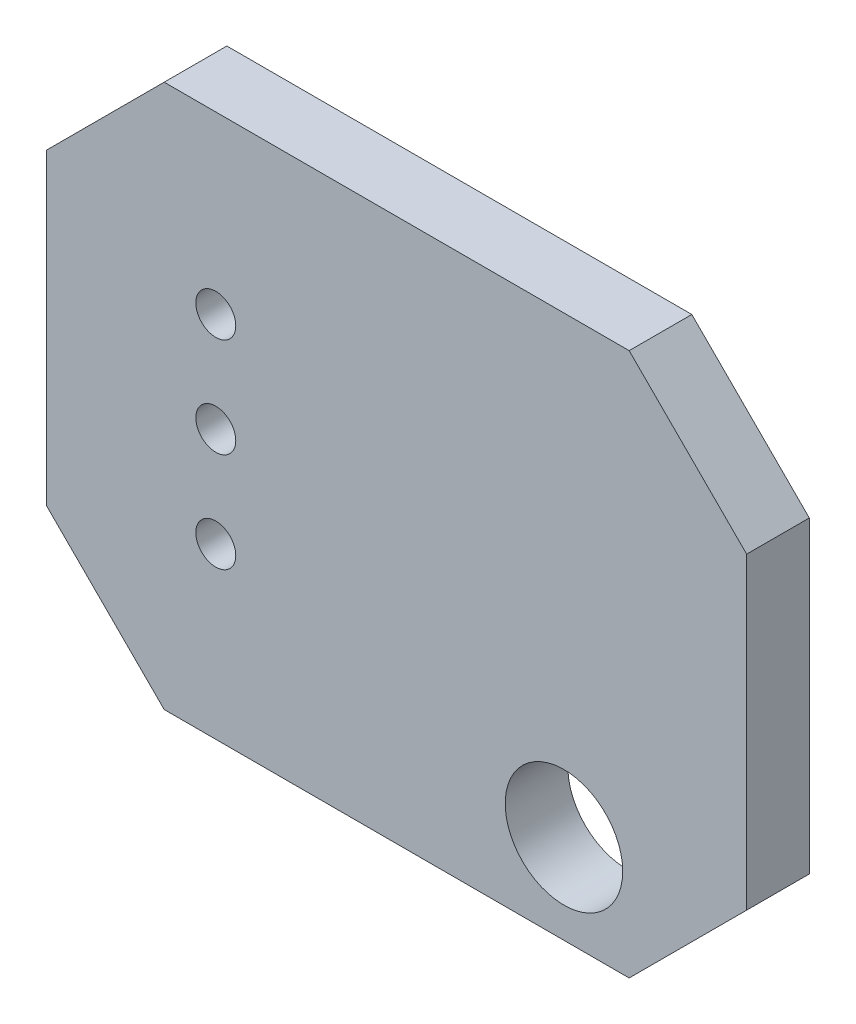
SolidWorks part; units mm, degrees
ref_plane "Face" through (0, 0, 0) normal (0, 0, 1) x (1, 0, 0)
ref_plane "Dessus" through (0, 0, 0) normal (0, 1, 0) x (1, 0, 0)
ref_plane "Droite" through (0, 0, 0) normal (1, 0, 0) x (0, 0, -1)
ref_plane "Dielectric_Layer Couche 1" through (0, 0, 1.6) normal (0, 0, 1) x (1, 0, 0)
sketch "Esquisse1" plane through (0, 0, 0) normal (0, 0, 1) x (1, 0, 0)
  line L0 (17.365, -1.778) -> (17.365, 12.095)
  line L1 (17.365, 12.095) -> (-0.508, 12.095)
  line L2 (-0.508, 12.095) -> (-0.508, -1.778)
  line L3 (-0.508, -1.778) -> (17.365, -1.778)
extrude "Board_Outline" add sketch "Esquisse1" along normal blind 1.6 separate body
sketch "Esquisse2" plane through (0, 0, 0) normal (0, 0, 1) x (1, 0, 0)
  circle A0 centre (12.7, 0.5) radius 1.5
extrude "NPTH" cut sketch "Esquisse2" along normal through all
sketch "Esquisse3" plane through (0, 0, 0) normal (0, 0, 1) x (1, 0, 0)
  circle A0 centre (3.81, 2.54) radius 0.51
  circle A1 centre (3.81, 5.08) radius 0.51
  circle A2 centre (3.81, 7.62) radius 0.51
extrude "PTH" cut sketch "Esquisse3" along normal through all
chamfer "Chanfrein1" distance 3 angle 45 4 edges at (-0.508, 12.095, 0.8) (-0.508, -1.778, 0.8) (17.365, -1.778, 0.8) (17.365, 12.095, 0.8)
